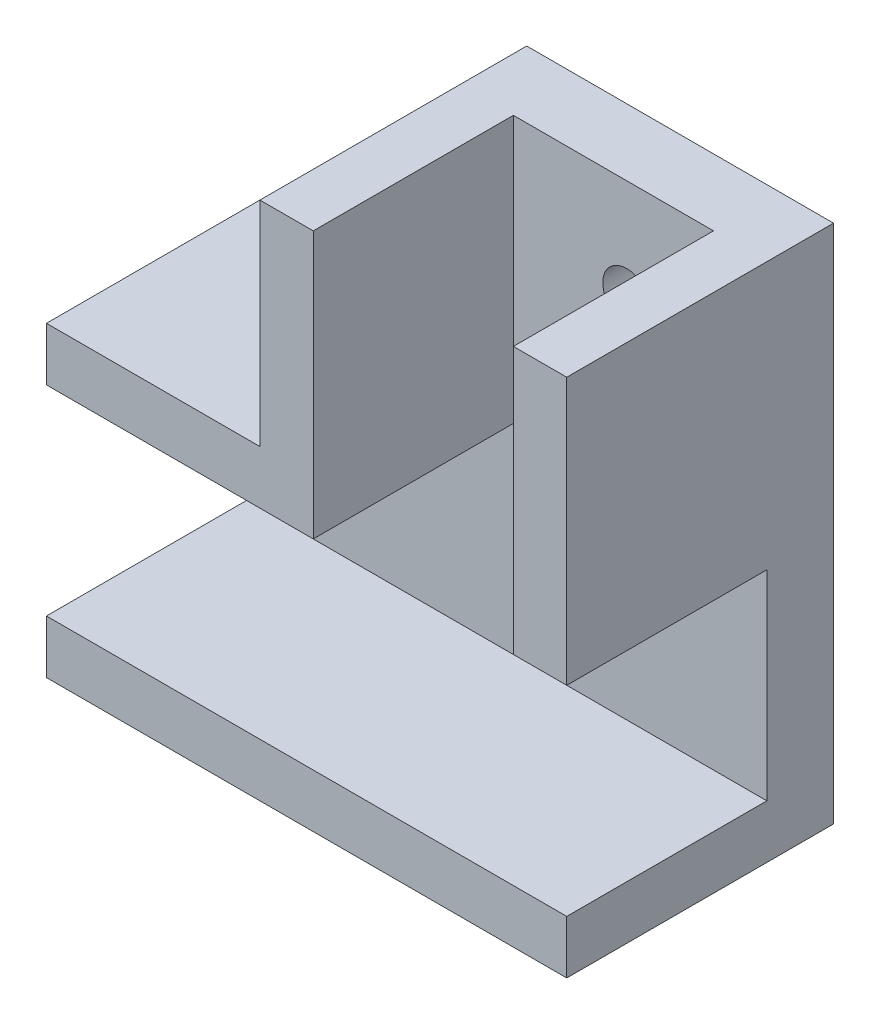
SolidWorks part; units mm, degrees
ref_plane "Front Plane" through (0, 0, 0) normal (0, 0, 1) x (1, 0, 0)
ref_plane "Top Plane" through (0, 0, 0) normal (0, 1, 0) x (1, 0, 0)
ref_plane "Right Plane" through (0, 0, 0) normal (1, 0, 0) x (0, 0, -1)
sketch "Sketch1" plane through (0, 0, 0) normal (0, 0, 1) x (1, 0, 0)
  line L1 (-20.6863, -4.2647) -> (-0.6863, -4.2647)
  line L2 (-20.6863, -4.2647) -> (-20.6863, -19.2647)
  line L3 (-20.6863, -19.2647) -> (14.3137, -19.2647)
  line L5 (-0.6863, 15.7353) -> (14.3137, 15.7353)
  line L6 (-0.6863, 15.7353) -> (-0.6863, -4.2647)
  line L8 (14.3137, 15.7353) -> (14.3137, -4.2647)
  line L9 (14.3137, -4.2647) -> (14.3137, -19.2647)
  dimension "D1" = 15
  dimension "D2" = 20
  dimension "D3" = 20
  dimension "D4" = 15
extrude "Boss-Extrude1" add sketch "Sketch1" along normal blind 5
sketch "Sketch2" plane through (0, 0, 0) normal (0, 0, -1) x (-1, 0, 0)
  line L0 (0.6863, 15.7353) -> (4.6863, 15.7353)
  line L1 (4.6863, 15.7353) -> (4.6863, -0.2647)
  line L2 (20.6863, -4.2647) -> (20.6863, -0.2647)
  line L3 (20.6863, -0.2647) -> (6.08, -0.2647)
  line L4 (20.6863, -4.2647) -> (0.6863, -4.2647)
  line L5 (0.6863, 15.7353) -> (0.6863, -4.2647)
  line L6 (6.08, -0.2647) -> (4.6863, -0.2647)
  dimension "D1" = 4
  dimension "D2" = 4
extrude "Boss-Extrude2" add sketch "Sketch2" against normal blind 20 contours L3 L6 L1 L0 L5 L4 L2
sketch "Sketch4" plane through (0, 0, 0) normal (0, 0, -1) x (-1, 0, 0)
  line L0 (20.6863, -19.2647) -> (-14.3137, -19.2647)
  line L2 (-14.3137, -23.2647) -> (20.6863, -23.2647)
  line L3 (20.6863, -23.2647) -> (20.6863, -19.2647)
  line L4 (-14.3137, -19.2647) -> (-14.3137, -23.2647)
  dimension "D1" = 4
extrude "Boss-Extrude3" add sketch "Sketch4" against normal blind 20
ref_plane "Plane4" through (7.8137, 0, 0) normal (-1, 0, 0) x (0, 0, 1)
ref_plane "Plane5" through (-4.6863, 0, 0) normal (-1, 0, 0) x (0, 0, 1)
sketch "Sketch6" plane through (0, 0, 5) normal (0, 0, 1) x (1, 0, 0)
  line L0 (7.8137, 8.8) -> (7.8137, -8.8) construction
  line L1 (-20.6863, -4.2647) -> (-20.6863, -19.2647) construction
  line L2 (-20.6863, -4.2647) -> (-0.6863, -4.2647) construction
  line L6 (14.3137, 15.7353) -> (-0.6863, 15.7353) construction
  circle A0 centre (7.8137, 8.2353) radius 1.8
  circle A1 centre (-13.1863, -11.7647) radius 1.8
  dimension "D1" = 3.6
  dimension "D2" = 3.6
  dimension "D5" = 7.5
  dimension "D8" = 7.5
  dimension "D4" = 7.5
ref_plane "Plane6" through (-4.6863, -0.2647, 20) normal (0, -1, 0) x (-1, 0, 0)
extrude "Cut-Extrude3" cut sketch "Sketch6" against normal through all
sketch "Sketch7" plane through (0, 0, 0) normal (0, 0, -1) x (-1, 0, 0)
  line L0 (-14.3137, -23.2647) -> (-14.3137, 15.7353) construction
  line L1 (-14.3137, 15.7353) -> (-18.3137, 15.7353)
  line L2 (-14.3137, 15.7353) -> (-14.3137, -23.2647)
  line L3 (-14.3137, -23.2647) -> (-18.3137, -23.2647)
  line L4 (-18.3137, 15.7353) -> (-18.3137, -23.2647)
  dimension "D1" = 4
  dimension "D2" = 39
extrude "Boss-Extrude4" add sketch "Sketch7" against normal blind 20
sketch "Sketch8" plane through (-20.6863, 0, 0) normal (-1, 0, 0) x (0, 0, 1)
  line L1 (5, -4.2647) -> (20, -4.2647)
  line L2 (5, -4.2647) -> (5, -19.2647)
  line L3 (5, -19.2647) -> (20, -19.2647)
  line L4 (20, -4.2647) -> (20, -19.2647)
extrude "Cut-Extrude4" cut sketch "Sketch8" against normal through all and the other way through all
